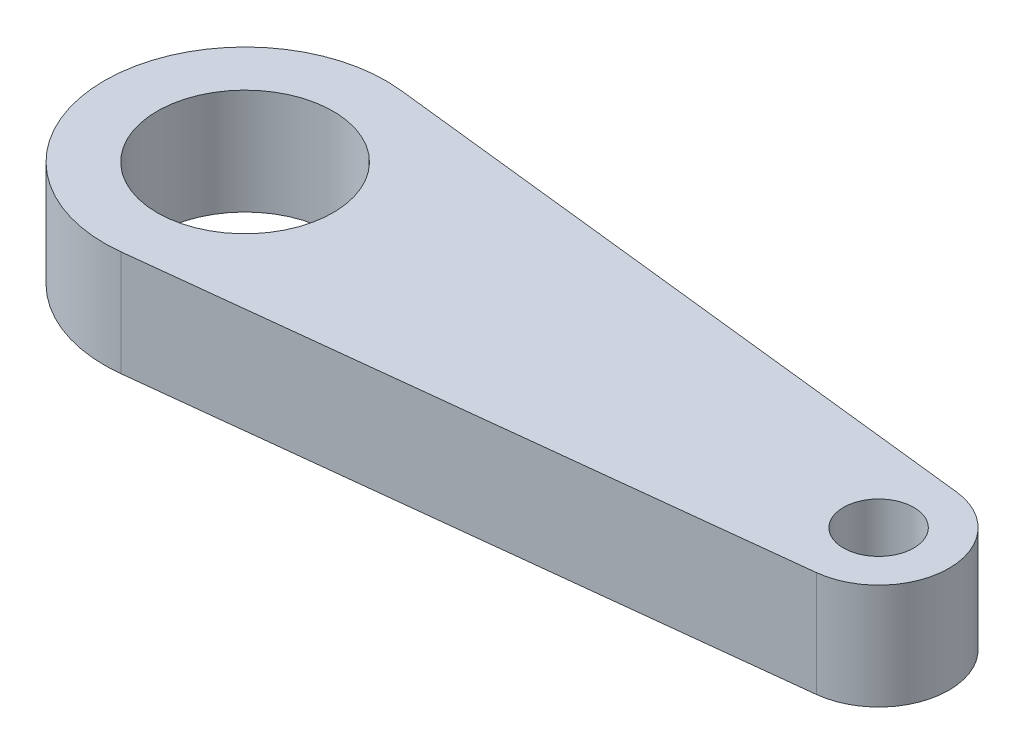
SolidWorks part; units mm, degrees
ref_plane "前视基准面" through (0, 0, 0) normal (0, 0, 1) x (1, 0, 0)
ref_plane "上视基准面" through (0, 0, 0) normal (0, 1, 0) x (1, 0, 0)
ref_plane "右视基准面" through (0, 0, 0) normal (1, 0, 0) x (0, 0, -1)
sketch "草图1" plane through (0, 0, 0) normal (0, 1, 0) x (1, 0, 0)
  line L0 (-29.1257, 0) -> (74.8601, 0) construction
  line L1 (18.2222, 1.9876) -> (0.4444, 3.9752)
  line L2 (18.2222, -1.9876) -> (0.4444, -3.9752)
  arc A0 (0.4444, 3.9752) -> (0.4444, -3.9752) centre (0, 0) ccw
  circle A1 centre (0, 0) radius 2.5
  arc A2 (18.2222, -1.9876) -> (18.2222, 1.9876) centre (18, 0) ccw
  circle A3 centre (18, 0) radius 1
  point P7 (46.121, 0)
  point P12 (74.8601, 0)
  point P13 (-29.1257, 0)
  dimension "D1" = 8
  dimension "D2" = 5
  dimension "D3" = 4
  dimension "D4" = 2
  dimension "D5" = 18
extrude "凸台-拉伸1" add sketch "草图1" along normal blind 3
